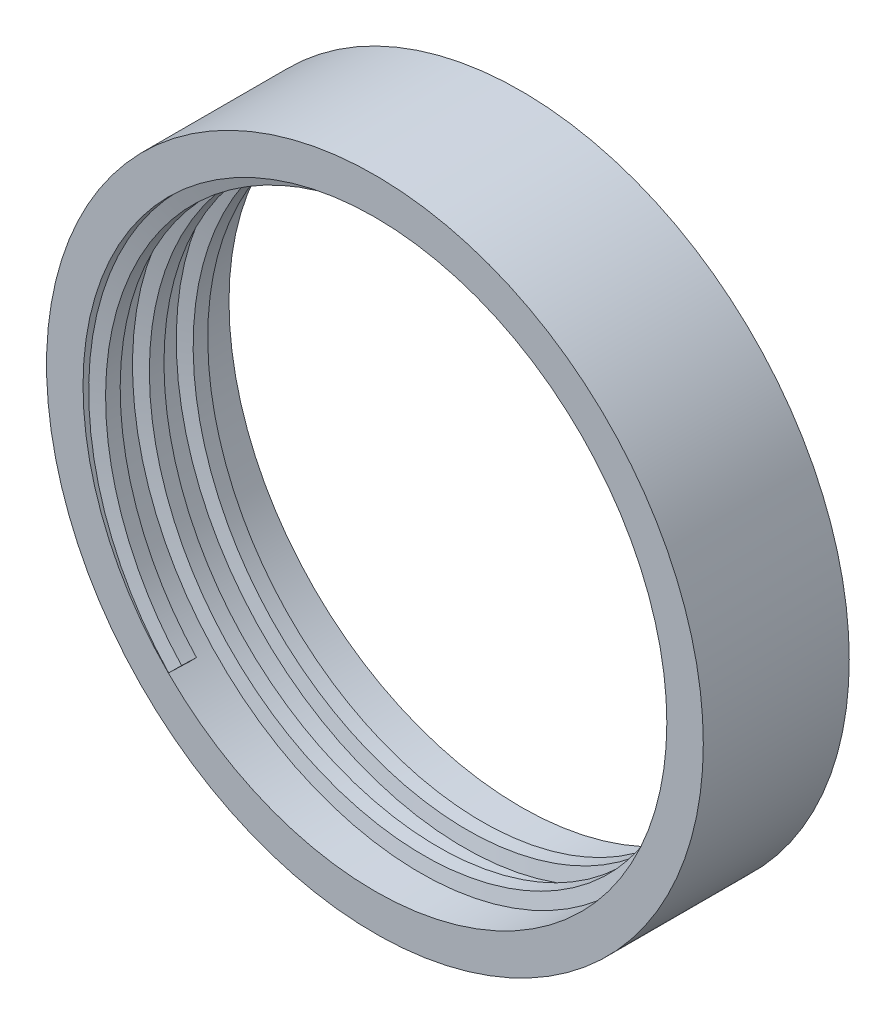
SolidWorks part; units mm, degrees
ref_plane "前视基准面" through (0, 0, 0) normal (0, 0, 1) x (1, 0, 0)
ref_plane "上视基准面" through (0, 0, 0) normal (0, 1, 0) x (1, 0, 0)
ref_plane "右视基准面" through (0, 0, 0) normal (1, 0, 0) x (0, 0, -1)
sketch "草图1" plane through (0, 0, 0) normal (0, 0, 1) x (1, 0, 0)
  circle A0 centre (0, 0) radius 45
  circle A1 centre (0, 0) radius 40
extrude "凸台-拉伸1" add sketch "草图1" along normal blind 20
ref_plane "基准面1" through (0, 0, 18.5) normal (0, 0, 1) x (1, 0, 0)
sketch "草图2" plane through (0, 0, 18.5) normal (0, 0, 1) x (1, 0, 0)
  circle A0 centre (0, 0) radius 40.15
curve "螺旋线/涡状线1" pitch 6 height 15 turns 2.5
ref_plane "基准面2" through (-28.3903, -28.3903, 18.5) normal (-0.7069, 0.7069, -0.0238) x (-0.0168, 0.0168, 0.9997)
sketch "草图3" plane through (-28.3903, -28.3903, 18.5) normal (-0.7069, 0.7069, -0.0238) x (-0.0168, 0.0168, 0.9997)
  line L0 (1.5, 0) -> (-1.5, 0)
  line L1 (1, 2) -> (-1, 2)
  line L2 (1.5, 0) -> (1, 2)
  line L3 (-1.5, 0) -> (-1, 2)
sweep "扫描1" add profiles "草图3" path "螺旋线/涡状线1"
